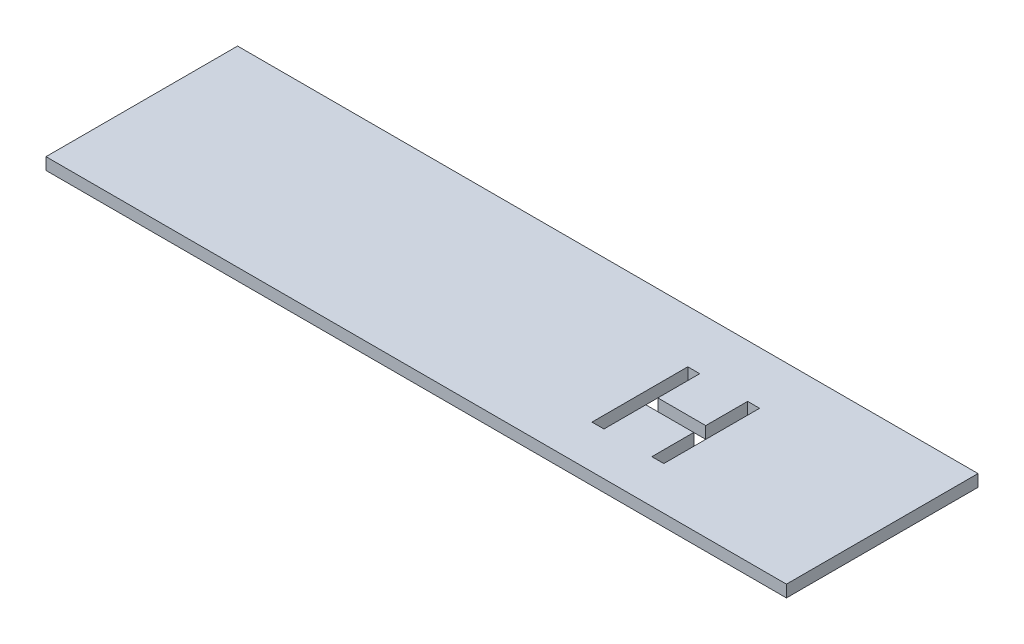
SolidWorks part; units mm, degrees
material "Plywood"
ref_plane "Front Plane" through (0, 0, 0) normal (0, 0, 1) x (1, 0, 0)
ref_plane "Top Plane" through (0, 0, 0) normal (0, 1, 0) x (1, 0, 0)
ref_plane "Right Plane" through (0, 0, 0) normal (1, 0, 0) x (0, 0, -1)
sketch "Sketch1" plane through (0, 0, 0) normal (0, 1, 0) x (1, 0, 0)
  line L1 (0, 0) -> (196.342, 0)
  line L2 (0, 0) -> (0, 50.8)
  line L3 (0, 50.8) -> (196.342, 50.8)
  line L4 (196.342, 0) -> (196.342, 50.8)
  dimension "D1" = 50.8
  dimension "D2" = 196.342
extrude "Boss-Extrude1" add sketch "Sketch1" along normal blind 3.175
sketch "Sketch2" plane through (0, 0, 0) normal (0, -1, 0) x (1, 0, 0)
  line L12 (136.525, -25.7175) -> (136.525, -36.83)
  line L13 (133.35, -11.43) -> (136.525, -11.43)
  line L14 (133.35, -11.43) -> (133.35, -36.83)
  line L15 (133.35, -36.83) -> (136.525, -36.83)
  line L16 (136.525, -11.43) -> (136.525, -22.5425)
  line L17 (149.225, -11.43) -> (152.4, -11.43)
  line L18 (149.225, -11.43) -> (149.225, -22.5425)
  line L19 (149.225, -36.83) -> (152.4, -36.83)
  line L20 (152.4, -11.43) -> (152.4, -36.83)
  line L21 (136.525, -22.5425) -> (149.225, -22.5425)
  line L23 (136.525, -25.7175) -> (149.225, -25.7175)
  line L25 (149.225, -25.7175) -> (149.225, -36.83)
  dimension "D1" = 12.7
  dimension "D2" = 25.4
  dimension "D3" = 25.4
  dimension "D4" = 3.175
  dimension "D5" = 3.175
  dimension "D6" = 11.1125
  dimension "D7" = 3.175
  dimension "D8" = 133.35
  dimension "D9" = 11.43
extrude "Cut-Extrude1" cut sketch "Sketch2" against normal blind 7.62
